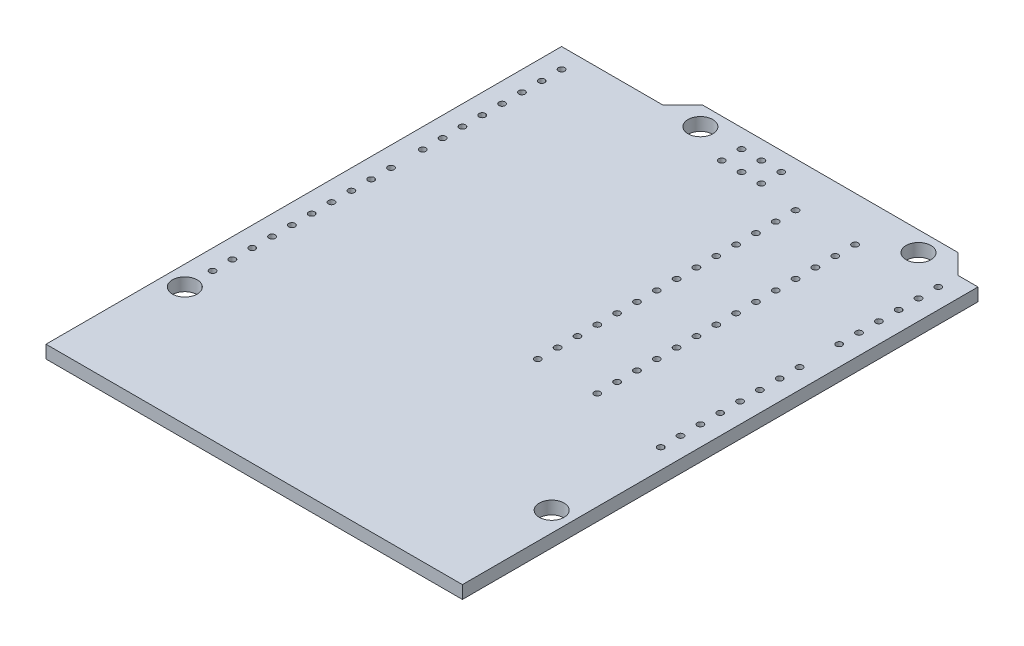
SolidWorks part; units mm, degrees
material "E-Glass Fiber"
ref_plane "Front Plane" through (0, 0, 0) normal (0, 0, 1) x (1, 0, 0)
ref_plane "Top Plane" through (0, 0, 0) normal (0, 1, 0) x (1, 0, 0)
ref_plane "Right Plane" through (0, 0, 0) normal (1, 0, 0) x (0, 0, -1)
sketch "Sketch1" plane through (0, 0, 0) normal (0, 1, 0) x (1, 0, 0)
  line L0 (-55, 0) -> (55, 0) construction
  line L1 (0, 0) -> (-53.34, 0)
  line L2 (0, 0) -> (0, 66.04)
  line L3 (-5.08, 68.58) -> (-37.846, 68.58)
  line L4 (-53.34, 0) -> (-53.34, 66.04)
  line L5 (-53.34, 66.04) -> (-40.386, 66.04)
  line L6 (-40.386, 66.04) -> (-37.846, 68.58)
  line L7 (-5.08, 68.58) -> (-2.54, 66.04)
  line L8 (-2.54, 66.04) -> (0, 66.04)
  circle A0 centre (-7.62, 66.04) radius 1.5875
  circle A1 centre (-35.56, 66.04) radius 1.5875
  circle A2 centre (-2.54, 13.97) radius 1.5875
  circle A3 centre (-50.8, 15.24) radius 1.5875
  dimension "D8" = 3.175
  dimension "D16" = 15.24
  dimension "D1" = 68.58
  dimension "D2" = 53.34
  dimension "D3" = 66.04
  dimension "D4" = 2.54
  dimension "D5" = 45
  dimension "D6" = 45
  dimension "D7" = 40.386
  dimension "D9" = 66.04
  dimension "D10" = 35.56
  dimension "D11" = 7.62
  dimension "D12" = 13.97
  dimension "D13" = 2.54
  dimension "D14" = 15.24
  dimension "D15" = 50.8
extrude "Boss-Extrude1" add sketch "Sketch1" against normal blind 1.65
sketch "Sketch2" plane through (0, 0, 0) normal (0, 1, 0) x (1, 0, 0)
  line L0 (0, -0.9075) -> (0, 0.9075) construction
  line L1 (-0.9075, 0) -> (0.9075, 0) construction
  circle A0 centre (-2.54, 27.94) radius 0.4
  dimension "D1" = 0.8
  dimension "D2" = 2.54
  dimension "D3" = 27.94
extrude "Cut-Extrude1" cut sketch "Sketch2" against normal blind 1.65
sketch "Sketch3" plane through (0, 0, 0) normal (0, 1, 0) x (1, 0, 0)
  line L0 (0, -0.9075) -> (0, 0.9075) construction
  line L1 (-0.9075, 0) -> (0.9075, 0) construction
  circle A0 centre (-50.8, 18.796) radius 0.4
  dimension "D2" = 0.8
  dimension "D1" = 50.8
  dimension "D3" = 18.796
extrude "Cut-Extrude2" cut sketch "Sketch3" against normal blind 1.65
pattern_linear "LPattern1" count 15 spacing 2.54 along (0, 0, -1) skipping (8, 0) of "Cut-Extrude1"
sketch "Sketch4" plane through (0, 0, 0) normal (0, 1, 0) x (1, 0, 0)
  line L0 (-0.9075, 0) -> (0.9075, 0) construction
  line L1 (0, -0.9075) -> (0, 0.9075) construction
  circle A0 centre (-50.8, 45.72) radius 0.4
  dimension "D3" = 0.8
  dimension "D1" = 45.72
  dimension "D2" = 50.8
extrude "Cut-Extrude3" cut sketch "Sketch4" against normal blind 1.65
pattern_linear "LPattern2" count 10 spacing 2.54 along (0, 0, -1) of "Cut-Extrude2"
pattern_linear "LPattern3" count 8 spacing 2.54 along (0, 0, -1) of "Cut-Extrude3"
sketch "Sketch5" plane through (0, 0, 0) normal (0, 1, 0) x (1, 0, 0)
  line L0 (-27.89, 66.18) -> (-27.89, 63.64) construction
  line L1 (-30.43, 66.18) -> (-25.35, 66.18) construction
  line L2 (-30.43, 66.18) -> (-30.43, 63.64) construction
  line L3 (-30.43, 63.64) -> (-25.35, 63.64) construction
  line L4 (-25.35, 66.18) -> (-25.35, 63.64) construction
  line L5 (-55, 0) -> (55, 0) construction
  line L6 (0, -55) -> (0, 55) construction
  circle A0 centre (-30.43, 66.18) radius 0.4
  circle A1 centre (-27.89, 66.18) radius 0.4
  circle A2 centre (-25.35, 66.18) radius 0.4
  circle A3 centre (-25.35, 63.64) radius 0.4
  circle A4 centre (-27.89, 63.64) radius 0.4
  circle A5 centre (-30.43, 63.64) radius 0.4
  circle A6 centre (-47.498, 399.9992) radius 0.4
  circle A7 centre (-47.498, 402.5392) radius 0.4
  circle A8 centre (-47.498, 405.0792) radius 0.4
  circle A9 centre (-44.958, 405.0792) radius 0.4
  circle A10 centre (-44.958, 402.5392) radius 0.4
  circle A11 centre (-44.958, 399.9992) radius 0.4
  circle A12 centre (-42.418, 402.5392) radius 0.4
  circle A13 centre (-42.418, 405.0792) radius 0.4
  circle A14 centre (-39.878, 405.0792) radius 0.4
  circle A15 centre (-39.878, 402.5392) radius 0.4
  circle A16 centre (-26.162, 421.2082) radius 0.5
  circle A17 centre (-26.162, 416.1282) radius 0.5
  dimension "D4" = 0.8
  dimension "D14" = 1
  dimension "D1" = 2.54
  dimension "D2" = 2.54
  dimension "D3" = 2.54
  dimension "D5" = 63.64
  dimension "D6" = 30.43
  dimension "D7" = 2.54
  dimension "D8" = 2.54
  dimension "D9" = 2.54
  dimension "D10" = 2.54
  dimension "D11" = 2.54
  dimension "D12" = 47.498
  dimension "D13" = 399.9992
  dimension "D15" = 5.08
  dimension "D16" = 416.1282
  dimension "D17" = 26.162
extrude "Cut-Extrude4" cut sketch "Sketch5" against normal blind 10
sketch "Sketch6" plane through (0, 0, 0) normal (0, 1, 0) x (1, 0, 0)
  line L0 (0, -55) -> (0, 55) construction
  line L1 (-55, 0) -> (55, 0) construction
  line L2 (-20.193, 29.845) -> (-20.193, 32.385) construction
  circle A0 centre (-20.193, 29.845) radius 0.4
  circle A1 centre (-12.573, 29.845) radius 0.4
  circle A2 centre (-20.193, 32.385) radius 0.4
  circle A3 centre (-12.573, 32.385) radius 0.4
  circle A4 centre (-20.193, 34.925) radius 0.4
  circle A5 centre (-12.573, 34.925) radius 0.4
  circle A6 centre (-20.193, 37.465) radius 0.4
  circle A7 centre (-12.573, 37.465) radius 0.4
  circle A8 centre (-20.193, 40.005) radius 0.4
  circle A9 centre (-12.573, 40.005) radius 0.4
  circle A10 centre (-20.193, 42.545) radius 0.4
  circle A11 centre (-12.573, 42.545) radius 0.4
  circle A12 centre (-20.193, 45.085) radius 0.4
  circle A13 centre (-12.573, 45.085) radius 0.4
  circle A14 centre (-20.193, 47.625) radius 0.4
  circle A15 centre (-12.573, 47.625) radius 0.4
  circle A16 centre (-20.193, 50.165) radius 0.4
  circle A17 centre (-12.573, 50.165) radius 0.4
  circle A18 centre (-20.193, 52.705) radius 0.4
  circle A19 centre (-12.573, 52.705) radius 0.4
  circle A20 centre (-20.193, 55.245) radius 0.4
  circle A21 centre (-12.573, 55.245) radius 0.4
  circle A22 centre (-20.193, 57.785) radius 0.4
  circle A23 centre (-12.573, 57.785) radius 0.4
  circle A24 centre (-20.193, 60.325) radius 0.4
  circle A25 centre (-12.573, 60.325) radius 0.4
  circle A26 centre (-20.193, 62.865) radius 0.4
  circle A27 centre (-12.573, 62.865) radius 0.4
  dimension "D1" = 0.8
  dimension "D2" = 7.62
  dimension "D3" = 12.573
  dimension "D4" = 29.845
  dimension "D6" = 2.54
  dimension "D5" = 14
extrude "Cut-Extrude5" cut sketch "Sketch6" against normal blind 10
equation "\"D13@Sketch5\"=0.001*25.4*620"
equation "\"D16@Sketch5\"=645*0.001*25.4"
